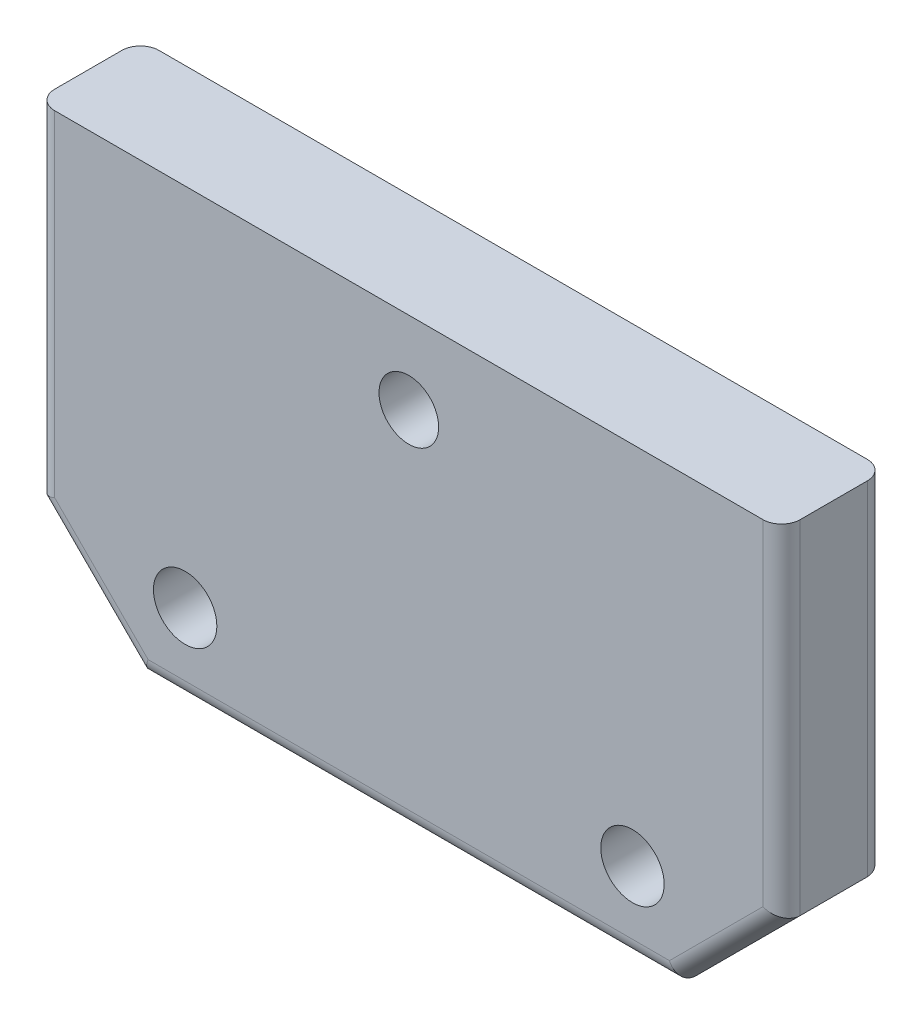
SolidWorks part; units mm, degrees
ref_plane "Front Plane" through (0, 0, 0) normal (0, 0, 1) x (1, 0, 0)
ref_plane "Top Plane" through (0, 0, 0) normal (0, 1, 0) x (1, 0, 0)
ref_plane "Right Plane" through (0, 0, 0) normal (1, 0, 0) x (0, 0, -1)
sketch "Sketch1" plane through (0, 0, 0) normal (0, 0, 1) x (1, 0, 0)
  line L0 (0, 0) -> (0, -10) construction
  line L3 (-50, -10) -> (50, -10)
  line L9 (-50, -10) -> (-50, 50)
  line L10 (-50, 50) -> (50, 50)
  line L11 (50, -10) -> (50, 50)
  circle A0 centre (30, 1) radius 4.25
  circle A1 centre (-30, 1) radius 4.25
  circle A2 centre (0, 39) radius 4
  point P0 (0, 0)
  point P1 (0, 0)
  point P3 (0, 0)
  point P14 (0, 0)
  point P15 (0, 0)
  point P18 (0, 0)
  dimension "D3" = 60
  dimension "D4" = 8.5
  dimension "D7" = 8
  dimension "D5" = 11
  dimension "D1" = 60
  dimension "D2" = 100
  dimension "D8" = 7
extrude "Boss-Extrude1" add sketch "Sketch1" along normal mid plane 14
sketch "Sketch2" plane through (0, 0, -7) normal (0, 0, -1) x (-1, 0, 0)
  circle A0 centre (-30, 1) radius 6.4573
  circle A1 centre (30, 1) radius 6.4573
  circle A2 centre (-30, 1) radius 4.25 construction
  dimension "D1" = 12.9147
extrude "Boss-Extrude2" add sketch "Sketch2" against normal blind 6
chamfer "Chamfer1" distance 14 angle 45 2 edges at (-50, -10, 0) (50, -10, 0)
fillet "Fillet2" radius 2.5 10 edges at (0, -10, 7) (0, -10, -7) (43, -3, 7) (43, -3, -7) (-43, -3, 7) (-43, -3, -7) (50, 27, 7) (50, 27, -7) (-50, 27, 7) (-50, 27, -7)
sketch "Sketch3" plane through (0, 0, -7) normal (0, 0, -1) x (-1, 0, 0)
  line L1 (15, 27.8811) -> (-15, 27.8811)
  line L2 (15, 27.8811) -> (15, 5.8811)
  line L3 (15, 5.8811) -> (-15, 5.8811)
  line L4 (-15, 27.8811) -> (-15, 5.8811)
  line L5 (15, 27.8811) -> (-15, 5.8811) construction
  line L6 (15, 5.8811) -> (-15, 27.8811) construction
  point P0 (0, 16.8811)
  point P5 (0, 16.8811)
  point P6 (0, 0)
  dimension "D1" = 30
  dimension "D2" = 22
extrude "Cut-Extrude1" cut sketch "Sketch3" against normal blind 6
sketch "Sketch4" plane through (0, -10, 0) normal (0, -1, 0) x (1, 0, 0)
  line L0 (-34.9645, 7) -> (34.9645, 7) construction
  line L1 (30, -1) -> (30, 5.7184) construction
  line L2 (34.25, -1) -> (25.75, -1) construction
  line L3 (0, 0) -> (0, 19.3873) construction
  line L4 (-30, -1) -> (-30, 5.7184) construction
  circle A0 centre (30, 1) radius 1.25
  circle A1 centre (-30, 1) radius 1.25
  dimension "D1" = 2.5
  dimension "D2" = 6
extrude "Cut-Extrude2" cut sketch "Sketch4" against normal blind 12
